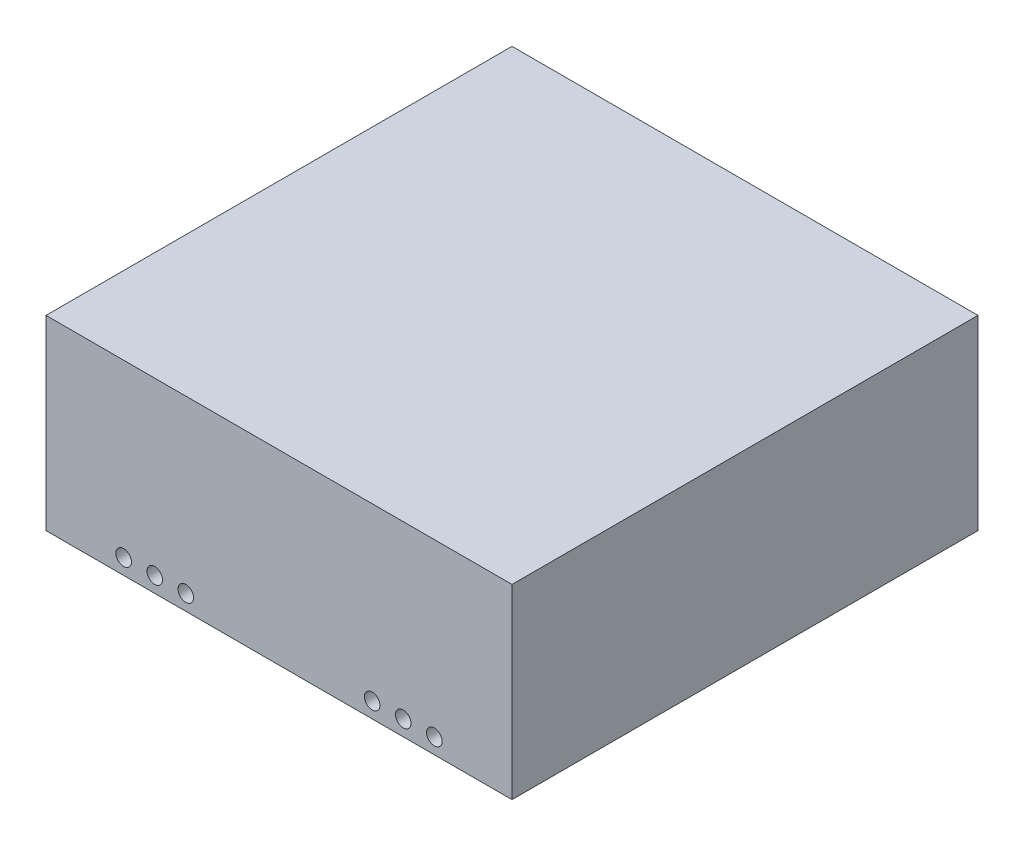
SolidWorks part; units mm, degrees
material "Cedar"
ref_plane "Front Plane" through (0, 0, 0) normal (0, 0, 1) x (1, 0, 0)
ref_plane "Top Plane" through (0, 0, 0) normal (0, 1, 0) x (1, 0, 0)
ref_plane "Right Plane" through (0, 0, 0) normal (1, 0, 0) x (0, 0, -1)
sketch "Sketch1" plane through (0, 0, 0) normal (0, 1, 0) x (1, 0, 0)
  line L1 (-75, 75) -> (75, 75)
  line L2 (-75, 75) -> (-75, -75)
  line L3 (-75, -75) -> (75, -75)
  line L4 (75, 75) -> (75, -75)
  line L5 (-75, 75) -> (75, -75) construction
  line L6 (-75, -75) -> (75, 75) construction
  point P0 (0, 0)
  dimension "D1" = 150
  dimension "D2" = 150
extrude "Boss-Extrude1" add sketch "Sketch1" along normal blind 60
shell "Shell1" thickness 7.5
sketch "Sketch5" plane through (0, 0, 75) normal (0, 0, 1) x (1, 0, 0)
  line L0 (75, 60) -> (75, 0) construction
  line L1 (-75, 60) -> (-75, 0) construction
  line L2 (-75, 0) -> (75, 0) construction
  circle A0 centre (-50, 5) radius 2.5
  circle A1 centre (-40, 5) radius 2.5
  circle A2 centre (-30, 5) radius 2.5
  circle A3 centre (30, 5) radius 2.5
  circle A4 centre (40, 5) radius 2.5
  circle A5 centre (50, 5) radius 2.5
  dimension "D1" = 5
  dimension "D2" = 5
  dimension "D3" = 5
  dimension "D4" = 5
  dimension "D5" = 5
  dimension "D6" = 5
  dimension "D7" = 10
  dimension "D8" = 10
  dimension "D9" = 10
  dimension "D10" = 10
  dimension "D11" = 25
  dimension "D12" = 25
  dimension "D13" = 5
  dimension "D14" = 5
  dimension "D15" = 5
  dimension "D16" = 5
  dimension "D17" = 5
  dimension "D18" = 5
extrude "Cut-Extrude2" cut sketch "Sketch5" against normal blind 10
sketch "Sketch6" plane through (0, 0, -75) normal (0, 0, -1) x (-1, 0, 0)
  line L0 (-75, 0) -> (75, 0) construction
  circle A0 centre (-14.5, 8) radius 1.5
  circle A1 centre (14.5, 8) radius 1.5
  dimension "D1" = 14.5
  dimension "D5" = 3
  dimension "D6" = 3
  dimension "D2" = 14.5
  dimension "D3" = 8
  dimension "D4" = 8
extrude "Cut-Extrude3" cut sketch "Sketch6" against normal blind 10
